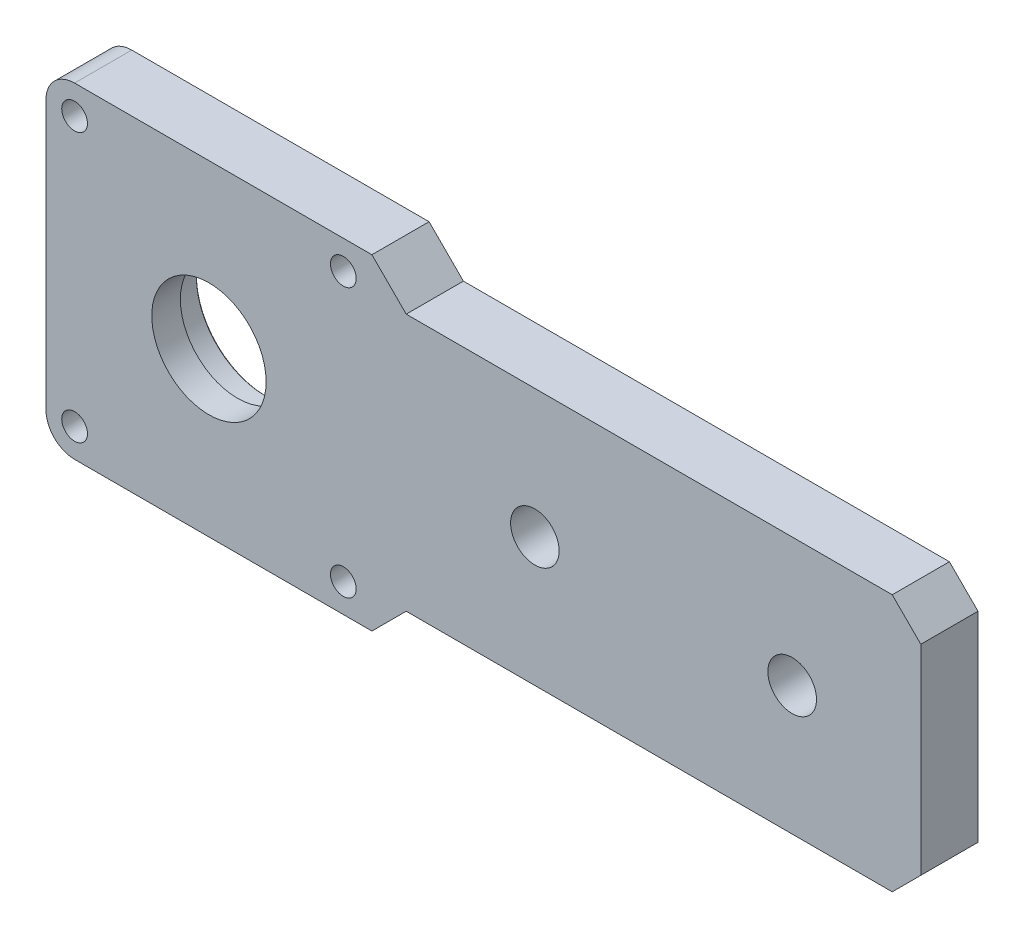
SolidWorks part; units mm, degrees
material "6061 合金"
ref_plane "前视基准面" through (0, 0, 0) normal (0, 0, 1) x (1, 0, 0)
ref_plane "上视基准面" through (0, 0, 0) normal (0, 1, 0) x (1, 0, 0)
ref_plane "右视基准面" through (0, 0, 0) normal (1, 0, 0) x (0, 0, -1)
sketch "草图1" plane through (0, 0, 0) normal (0, 0, 1) x (1, 0, 0)
  line L0 (28.5, -28.5) -> (34.5, -22.5)
  line L1 (-28.5, -28.5) -> (28.5, -28.5)
  line L2 (-28.5, -28.5) -> (-28.5, 28.5)
  line L3 (-28.5, 28.5) -> (28.5, 28.5)
  line L4 (28.5, -28.5) -> (28.5, 28.5)
  line L5 (-28.5, -28.5) -> (28.5, 28.5) construction
  line L6 (-28.5, 28.5) -> (28.5, -28.5) construction
  line L7 (124.5, -22.5) -> (28.5, -22.5)
  line L8 (124.5, -22.5) -> (124.5, 22.5)
  line L9 (124.5, 22.5) -> (28.5, 22.5)
  line L10 (28.5, -22.5) -> (28.5, 22.5)
  line L11 (124.5, -22.5) -> (28.5, 22.5) construction
  line L12 (124.5, 22.5) -> (28.5, -22.5) construction
  line L13 (124.5, 0) -> (-55.3636, 0) construction
  line L14 (28.5, 28.5) -> (34.5, 22.5)
  point P0 (0, 0)
  point P6 (76.5, 0)
  dimension "D1" = 63
  dimension "D2" = 57
  dimension "D3" = 45
  dimension "D4" = 90
  dimension "D5" = 45
extrude "凸台-拉伸1" add sketch "草图1" along normal mid plane 10
sketch "草图6" plane through (0, 0, 5) normal (0, 0, 1) x (1, 0, 0)
  circle A0 centre (0, 0) radius 10
  dimension "D1" = 20
extrude "过孔" cut sketch "草图6" against normal blind 10
sketch "草图19" plane through (0, 0, -5) normal (0, 0, -1) x (-1, 0, 0)
  circle A0 centre (0, 0) radius 12
  dimension "D1" = 24
extrude "轴承孔" cut sketch "草图19" against normal blind 5
hole_wizard "Ø8.5 (8.5) 直径孔1" positions "草图5" profile "草图4" hole size "Ø8.5" standard "GB" end condition through all
sketch "草图5" plane through (0, 0, 5) normal (0, 0, 1) x (1, 0, 0)
  line L1 (79.5, -22.5) -> (79.5, 22.5) construction
  line L2 (124.5, -22.5) -> (34.5, -22.5) construction
  line L3 (124.5, 22.5) -> (34.5, 22.5) construction
  line L5 (0, 0) -> (120.0042, 0) construction
  point P0 (57, 0)
  point P3 (102, 0)
  dimension "D1" = 45
sketch "草图4" plane through (57, 0, 5) normal (1, 0, 0) x (0, -1, 0)
  line L0 (0, 0) -> (0, 10)
  line L1 (0, 10) -> (4.25, 10)
  line L2 (4.25, 10) -> (4.25, 0)
  line L5 (4.25, 0) -> (0, 0)
  line L11 (0, -6.35) -> (0, 107.95) construction
  dimension "通孔孔直径" = 8.5
  dimension "通孔孔深度" = 10
hole_wizard "打孔尺寸(%根据)内六角圆柱头螺钉的类型1" positions "草图12" profile "草图11" counterbore size "M4" standard "GB" end condition through all
sketch "草图12" plane through (0, 0, -5) normal (0, 0, -1) x (-1, 0, 0)
  line L0 (0, 0) -> (0, -49.1013) construction
  line L2 (0, 0) -> (52.852, 0) construction
  point P0 (-23.5, 23.5)
  point P3 (23.5, 23.5)
  point P6 (23.5, -23.5)
  point P9 (-23.5, -23.5)
  dimension "D1" = 47
  dimension "D2" = 47
sketch "草图11" plane through (23.5, 23.5, -5) normal (1, 0, 0) x (0, 1, 0)
  line L0 (0, 0) -> (0, 10)
  line L1 (0, 10) -> (2.25, 10)
  line L3 (2.25, 10) -> (2.25, 4.6)
  line L4 (2.25, 4.6) -> (4, 4.6)
  line L5 (4, 4.6) -> (4, 0)
  line L7 (4, 0) -> (0, 0)
  line L11 (0, -6.35) -> (0, 107.95) construction
  dimension "通孔孔直径" = 4.5
  dimension "通孔孔深度" = 10
  dimension "柱形沉头孔直径" = 8
  dimension "柱形沉头孔深度" = 4.6
fillet "圆角1" radius 5 2 edges at (-28.5, 28.5, 0) (-28.5, -28.5, 0)
chamfer "倒角1" distance 5 angle 45 2 edges at (124.5, 22.5, 0) (124.5, -22.5, 0)
chamfer "倒角2" distance 0.2 angle 45 1 edges at (-12, 0, -5)
hole_wizard "M4 螺纹孔1" positions "草图21" profile "草图20" tap size "M4" standard "GB"
sketch "草图21" plane through (-28.5, 0, 0) normal (-1, 0, 0) x (0, 0, 1)
  line L0 (0, 0) -> (17.4295, 0) construction
  line L2 (0, 28.5) -> (0, -28.5) construction
  line L3 (-5, 28.5) -> (5, 28.5) construction
  line L4 (5, -28.5) -> (-5, -28.5) construction
  point P0 (0, 12.5)
  point P2 (0, -12.5)
  dimension "D1" = 25
sketch "草图20" plane through (-28.5, 12.5, 0) normal (0, 1, 0) x (0, 0, 1)
  line L0 (0, 0) -> (0, 15.5)
  line L1 (0, 15.5) -> (1.65, 15.5)
  line L2 (1.65, 15.5) -> (1.65, 0.2165)
  line L3 (1.65, 0.2165) -> (2.025, 0)
  line L5 (2.025, 0) -> (0, 0)
  line L6 (-1.65, 0.2165) -> (-2.025, 0) construction
  line L10 (0, 15.5) -> (-1.65, 15.5) construction
  line L11 (0, -6.35) -> (0, 107.95) construction
  dimension "螺纹孔钻头直径" = 3.3
  dimension "螺纹孔钻头深度" = 15.5
  dimension "近端锥形沉头孔直径" = 4.05
  dimension "近端锥形沉头孔角度" = 120
  dimension "导头角度" = 180
cosmetic thread "孔螺蚊线1" parameters "D1"=12, "D2"=4
cosmetic thread "孔螺蚊线2" parameters "D1"=12, "D2"=4
